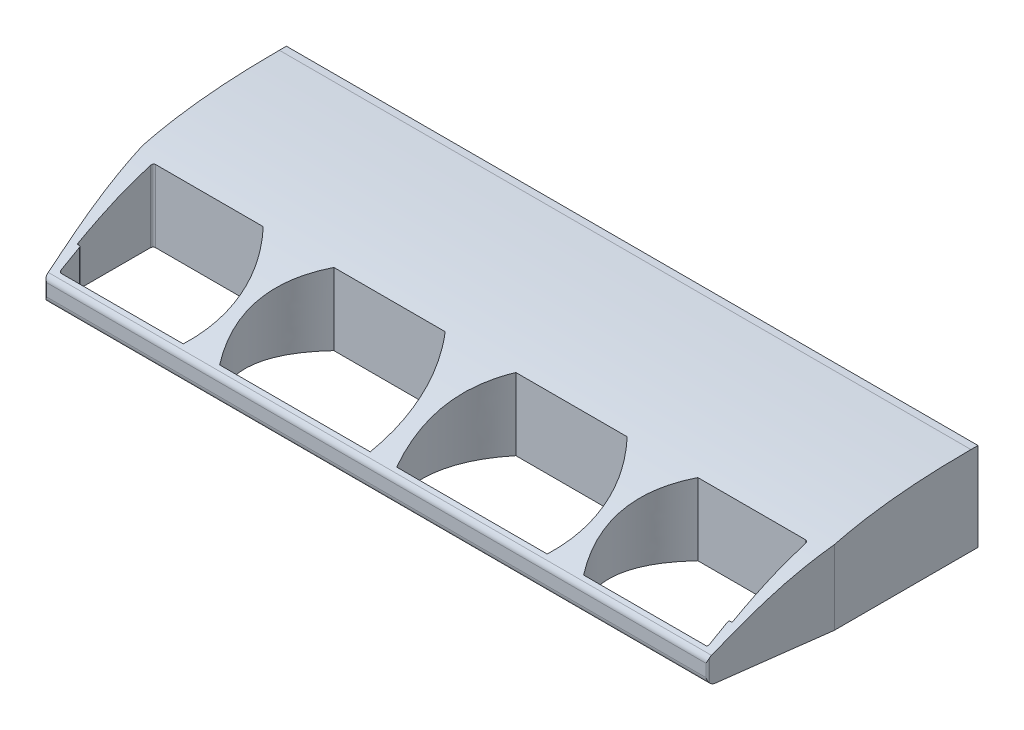
SolidWorks part; units mm, degrees
ref_plane "Front Plane" through (0, 0, 0) normal (0, 0, 1) x (1, 0, 0)
ref_plane "Top Plane" through (0, 0, 0) normal (0, 1, 0) x (1, 0, 0)
ref_plane "Right Plane" through (0, 0, 0) normal (1, 0, 0) x (0, 0, -1)
sketch "Sketch2" plane through (0, 0, 0) normal (0, 1, 0) x (1, 0, 0)
  line L0 (18.4137, 0) -> (18.5, 0)
  line L1 (18.55, 0.05) -> (18.55, 4.15)
  line L2 (-2, 4.3) -> (-8.3079, 4.3)
  line L3 (2, 4.3) -> (8.3079, 4.3)
  line L4 (-19.5879, 4.75) -> (-19.5879, 12.8912)
  line L5 (0, 11.25) -> (0, 4.3) construction
  line L6 (-0.75, -1.2) -> (-9.2772, -1.2)
  line L7 (9.2772, -1.2) -> (0.75, -1.2)
  line L8 (18.3637, -0.05) -> (18.3637, -1.1)
  line L9 (18.2637, -1.2) -> (11.3386, -1.2)
  line L10 (18.6712, -1.6013) -> (-18.6712, -1.6013)
  line L11 (19.5879, 4.75) -> (18.7703, -1.5142)
  line L12 (19.5879, 4.75) -> (19.5879, 12.8912)
  line L13 (19.5879, 12.8912) -> (-19.5879, 12.8912)
  line L14 (-12.3079, 4.3) -> (-18.4, 4.3)
  line L15 (-19.5879, 4.75) -> (-18.7703, -1.5142)
  line L16 (-18.3637, -0.05) -> (-18.3637, -1.1)
  line L17 (-18.5, 0) -> (-18.4137, 0)
  line L18 (-11.3386, -1.2) -> (-18.2637, -1.2)
  line L20 (-18.55, 0.05) -> (-18.55, 4.15)
  line L21 (8.3079, 4.3) -> (2, 4.3)
  line L22 (18.4, 4.3) -> (12.3079, 4.3)
  arc A0 (-18.4, 4.3) -> (-18.55, 4.15) centre (-18.4, 4.15) ccw
  arc A1 (18.4137, 0) -> (18.3637, -0.05) centre (18.4137, -0.05) ccw
  arc A2 (18.5, 0) -> (18.55, 0.05) centre (18.5, 0.05) ccw
  arc A3 (18.6712, -1.6013) -> (18.7703, -1.5142) centre (18.6712, -1.5013) ccw
  arc A4 (18.2637, -1.2) -> (18.3637, -1.1) centre (18.2637, -1.1) ccw
  arc A5 (-18.2637, -1.2) -> (-18.3637, -1.1) centre (-18.2637, -1.1) cw
  arc A6 (-18.6712, -1.6013) -> (-18.7703, -1.5142) centre (-18.6712, -1.5013) cw
  arc A7 (-18.5, 0) -> (-18.55, 0.05) centre (-18.5, 0.05) cw
  arc A8 (-18.4137, 0) -> (-18.3637, -0.05) centre (-18.4137, -0.05) cw
  arc A9 (18.55, 4.15) -> (18.4, 4.3) centre (18.4, 4.15) ccw
  spline S0 degree 2 poles (2, 4.3) (-0.1663, 1.6505) (0.75, -1.2) knots 0 0 0 1 1 1
  spline S1 degree 2 poles (-2, 4.3) (0.1663, 1.6505) (-0.75, -1.2) knots 0 0 0 1 1 1
  spline S2 degree 2 poles (12.3079, 4.3) (9.6374, 1.4403) (11.3386, -1.2) knots 0 0 0 1 1 1
  spline S3 degree 2 poles (8.3079, 4.3) (10.9784, 1.4403) (9.2772, -1.2) knots 0 0 0 1 1 1
  spline S4 degree 2 poles (-8.3079, 4.3) (-10.9784, 1.4403) (-9.2772, -1.2) knots 0 0 0 1 1 1
  spline S5 degree 2 poles (-12.3079, 4.3) (-9.6374, 1.4403) (-11.3386, -1.2) knots 0 0 0 1 1 1
  point P13 (-18.3637, 0)
  point P15 (18.3637, 0)
  point P19 (0, -1.2)
  point P28 (-18.55, 4.3)
  point P40 (18.55, 4.3)
  point P42 (0, 12.8912)
  point P43 (0, -1.6013)
  dimension "D2" = 4
  dimension "D1" = 0.15
  dimension "D4" = 2
extrude "Boss-Extrude1" add sketch "Sketch2" along normal blind 5
sketch "Sketch5" plane through (0, 5, 0) normal (0, 1, 0) x (1, 0, 0)
  line L0 (-19.5879, 4.75) -> (19.5879, 4.75)
  line L1 (-19.5879, 4.75) -> (-19.5879, -6.3843)
  line L2 (19.5879, 4.75) -> (19.5879, -6.3843)
  line L3 (-19.5879, -6.3843) -> (19.5879, -6.3843)
  line L4 (-19.5879, 4.75) -> (-18.7703, -1.5142) construction
  line L5 (-19.5879, 4.75) -> (-19.5879, 12.8912) construction
  line L6 (19.5879, 4.75) -> (18.7703, -1.5142) construction
  point P10 (-19.5879, -6.3843)
revolve "Cut-Revolve3" cut sketch "Sketch5" angle 30 about L0
sketch "Sketch8" plane through (-19.5879, 0, 0) normal (-1, 0, 0) x (0, 0, 1)
  line L0 (-12.8912, 0.4) -> (-12.8912, 4.6)
  line L2 (0.2095, 2.1366) -> (1.4013, 1.4485)
  line L3 (1.6013, 1.1021) -> (1.6013, 0.4)
  line L4 (1.2013, 0) -> (-12.4912, 0)
  line L5 (-12.4912, 5) -> (-4.75, 5) construction
  line L7 (-4.75, 5) -> (-2.3956, 3.6407) construction
  line L8 (-2.3956, 3.6407) -> (0.2095, 2.1366) construction
  line L9 (0.2095, 2.1366) -> (1.4013, 1.4485) construction
  line L10 (-14.2131, 7.9257) -> (4.2305, 7.1112)
  line L11 (4.2305, 7.1112) -> (3.5474, -3.8446)
  line L12 (3.5474, -3.8446) -> (-16.8666, -3.1352)
  line L13 (-16.8666, -3.1352) -> (-14.2131, 7.9257)
  arc A0 (1.4013, 1.4485) -> (1.6013, 1.1021) centre (1.2013, 1.1021) cw
  arc A1 (1.6013, 0.4) -> (1.2013, 0) centre (1.2013, 0.4) cw
  arc A2 (-12.8912, 4.6) -> (-12.4912, 5) centre (-12.4912, 4.6) cw
  arc A3 (-12.8912, 0.4) -> (-12.4912, 0) centre (-12.4912, 0.4) ccw
  spline S0 degree 4 poles (-12.4912, 5) (-4.75, 5) (-2.3956, 3.6407) (0.2095, 2.1366) (1.4013, 1.4485) knots 0 0 0 0 0 1 1 1 1 1
  point P12 (1.6013, 1.3331)
  point P15 (1.6013, 0)
  point P18 (-12.8912, 5)
  point P21 (-12.8912, 0)
  dimension "D1" = 0.4
extrude "Cut-Extrude2" cut sketch "Sketch8" against normal blind 50
